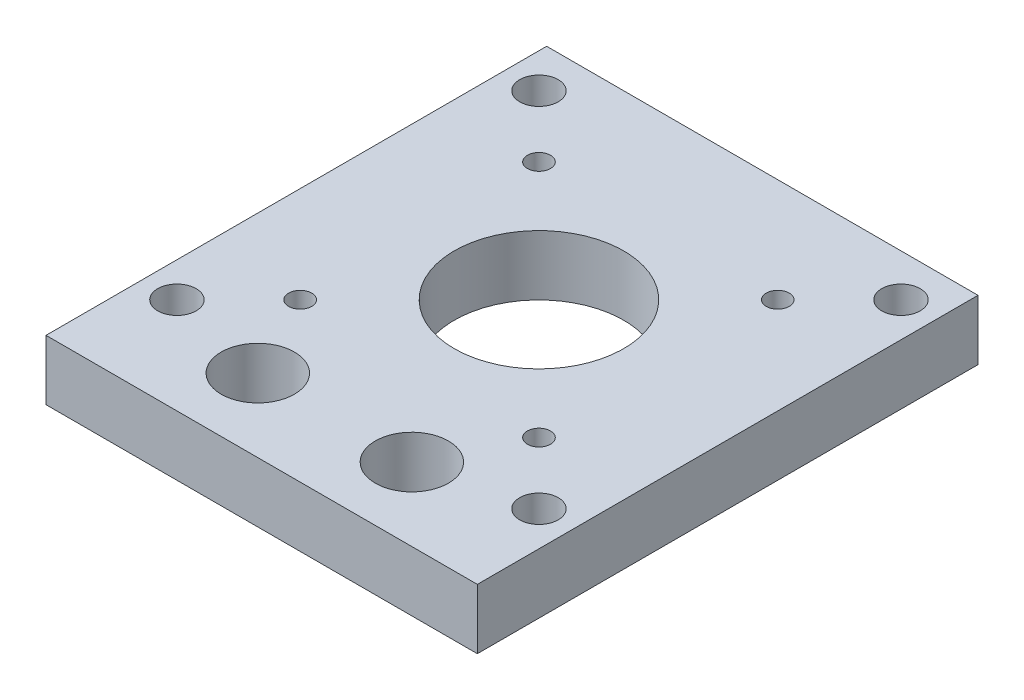
SolidWorks part; units mm, degrees
ref_plane "前视基准面" through (0, 0, 0) normal (0, 0, 1) x (1, 0, 0)
ref_plane "上视基准面" through (0, 0, 0) normal (0, 1, 0) x (1, 0, 0)
ref_plane "右视基准面" through (0, 0, 0) normal (1, 0, 0) x (0, 0, -1)
sketch "草图1" plane through (0, 0, 0) normal (0, 1, 0) x (1, 0, 0)
  line L1 (-28, 32.5) -> (28, 32.5)
  line L2 (-28, 32.5) -> (-28, -32.5)
  line L3 (-28, -32.5) -> (28, -32.5)
  line L4 (28, 32.5) -> (28, -32.5)
  line L5 (-28, 32.5) -> (28, -32.5) construction
  line L6 (-28, -32.5) -> (28, 32.5) construction
  point P0 (0, 0)
  dimension "D1" = 56
  dimension "D2" = 65
extrude "凸台-拉伸1" add sketch "草图1" along normal blind 7.8
sketch "草图3" plane through (0, 7.8, 0) normal (0, 1, 0) x (1, 0, 0)
  line L0 (0, 0) -> (0, -35.9071) construction
  line L2 (-28, -32.5) -> (28, -32.5) construction
  circle A0 centre (-10, -23) radius 4.75
  circle A1 centre (10, -23) radius 4.75
  dimension "D1" = 9.5
  dimension "D2" = 20
  dimension "D3" = 9.5
extrude "切除-拉伸2" cut sketch "草图3" against normal through all
sketch "草图4" plane through (0, 7.8, 0) normal (0, 1, 0) x (1, 0, 0)
  line L0 (-28, -32.5) -> (28, -32.5) construction
  line L1 (0, 3.5) -> (0, 35.4552) construction
  line L2 (0, 3.5) -> (34.2692, 3.5) construction
  circle A0 centre (0, 3.5) radius 11
  circle A1 centre (-15.5, 19) radius 1.5
  circle A2 centre (15.5, 19) radius 1.5
  circle A3 centre (15.5, -12) radius 1.5
  circle A4 centre (-15.5, -12) radius 1.5
  circle A5 centre (-23.5, 27) radius 2.5
  circle A6 centre (23.5, 27) radius 2.5
  circle A7 centre (23.5, -20) radius 2.5
  circle A8 centre (-23.5, -20) radius 2.5
  dimension "D2" = 22
  dimension "D3" = 3
  dimension "D6" = 5
  dimension "D1" = 36
  dimension "D4" = 31
  dimension "D5" = 31
  dimension "D7" = 47
  dimension "D8" = 47
extrude "切除-拉伸3" cut sketch "草图4" against normal through all
